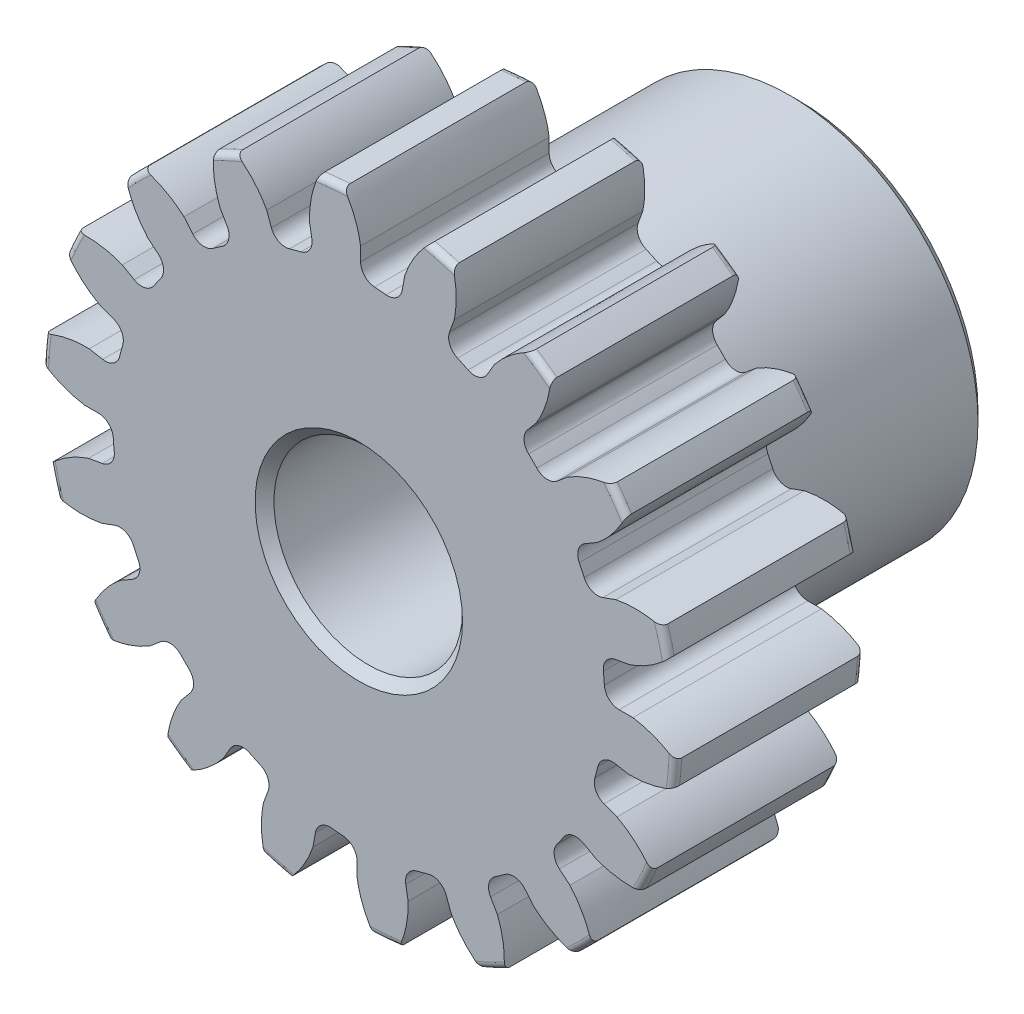
SolidWorks part; units mm, degrees
ref_plane "Front" through (0, 0, 0) normal (0, 0, 1) x (1, 0, 0)
ref_plane "Top" through (0, 0, 0) normal (0, 1, 0) x (1, 0, 0)
ref_plane "Right" through (0, 0, 0) normal (1, 0, 0) x (0, 0, -1)
sketch "Sketch1" plane through (0, 0, 0) normal (0, 0, 1) x (1, 0, 0)
  line L0 (-228.6, 0) -> (228.6, 0) construction
  circle A0 centre (0, 0) radius 8.001
  circle A1 centre (0, 0) radius 7.1501 construction
  circle A3 centre (0, 0) radius 6.2135 construction
  dimension "D1" = 1.7875
  dimension "OD" = 16.002
  dimension "Ptich Dia" = 14.3002
  dimension "Root Dia" = 12.4269
  dimension "D3" = 0.8509
  dimension "Number of Teeth" = 457.2
extrude "Boss-Extrude1" add sketch "Sketch1" against normal blind 4.7625
sketch "Sketch2" plane through (0, 0, 0) normal (1, 0, 0) x (0, 0, -1)
  line L0 (4.7625, 0) -> (11.1125, 0)
  line L1 (4.7625, 0) -> (4.7625, 4.7625)
  line L2 (4.7625, 4.7625) -> (11.1125, 4.7625)
  line L3 (11.1125, 4.7625) -> (11.1125, 0)
  point P5 (11.1125, -4.7625)
  point P6 (0, -8.001)
  point P7 (4.7625, -8.001)
  point P9 (0, 8.001)
  dimension "Face Wd" = 4.7625
  dimension "B Hub Dia" = 9.525
  dimension "D O'all Lg." = 11.1125
revolve "Revolve1" add sketch "Sketch2" angle 360 about L0
fillet "Fillet2" radius 0.16 3 edges at (8.001, 0, -4.7625) (8.001, 0, 0) (4.7625, 0, -4.7625)
sketch "Sketch3" plane through (0, 0, 0) normal (0, 0, 1) x (1, 0, 0)
  line L0 (0, 0) -> (0, 8.001) construction
  line L1 (-1.7332, 6.7019) -> (0, 7.1501)
  line L2 (-9.5921, 7.1501) -> (9.5921, 7.1501) construction
  line L3 (-9.2865, 4.7484) -> (9.2865, 9.5518) construction
  line L4 (-1.7332, 6.7019) -> (0, 0) construction
  line L5 (-4.4209, 5.3268) -> (0, 0) construction
  line L6 (-4.4209, 5.3268) -> (-0.7209, 8.3975) construction
  line L7 (-1.2086, 6.816) -> (0, 0) construction
  line L8 (-1.2086, 6.816) -> (0.0254, 7.0348) construction
  arc A0 (-1.7332, 6.7019) -> (-4.4209, 5.3268) centre (0, 0) ccw
  circle A1 centre (0, 0) radius 7.1501 construction
  circle A2 centre (0, 0) radius 6.9224 construction
  arc A3 (-1.7332, 6.7019) -> (-1.2086, 6.816) centre (0, 0) cw
  circle A4 centre (0, 0) radius 8.001 construction
  point P6 (0, 7.1501)
  dimension "D1" = 1.7902
  dimension "Pressure Angle" = 14.5
  dimension "D2" = 3.0434
  dimension "D3" = 4.8083
  dimension "D4" = 0.5371
  dimension "D5" = 1.2532
sketch "Sketch4" plane through (0, 0, 0) normal (0, 0, 1) x (1, 0, 0)
  line L0 (0, 0) -> (0.6208, 7.0958) construction
  line L1 (0.0448, 6.9222) -> (0.0448, 6.2133)
  line L2 (0, 7.1501) -> (1.2416, 7.0415) construction
  line L3 (1.1579, 6.8248) -> (1.0348, 6.1267)
  line L4 (0.0448, 6.2133) -> (0, 0) construction
  line L5 (0, 0) -> (0, 8.001) construction
  line L6 (-4.4209, 5.3268) -> (-0.7209, 8.3975) construction
  line L7 (-4.4209, 5.3268) -> (-0.7209, 8.3975) construction
  arc A0 (1.0348, 6.1267) -> (0.0448, 6.2133) centre (0, 0) ccw
  arc A1 (0, 7.1501) -> (1.2416, 7.0415) centre (0, 0) cw construction
  circle A2 centre (0, 0) radius 7.1501 construction
  circle A3 centre (0, 0) radius 6.9224 construction
  circle A4 centre (0, 0) radius 6.2135 construction
  arc A5 (2.1681, 8.1448) -> (-0.7209, 8.3975) centre (0, 0) ccw
  spline S0 degree 2 poles (-0.7209, 8.3975) (-0.0794, 7.7502) (0.0448, 6.9222) knots 0 0 0 1 1 1
  spline S1 degree 2 poles (2.1681, 8.1448) (1.424, 7.6187) (1.1579, 6.8248) knots 0 0 0 1 1 1
  dimension "D1" = 1.2479
extrude "Cut-Extrude1" cut sketch "Sketch4" against normal through all
fillet "Fillet1" radius 0.3744 2 edges at (1.0348, 6.1267, -2.3813) (0.0448, 6.2133, -2.3813)
pattern_circular "CirPattern1" count 18 over 360 about axis through (0, 0, -4.7625) along (0, 0, 1) of "Cut-Extrude1", "Fillet1"
sketch "Sketch5" plane through (0, 0, 0) normal (0, 0, 1) x (1, 0, 0)
  circle A0 centre (0, 0) radius 2.3813
  circle A1 centre (0, 0) radius 1.5875 construction
  dimension "Bore Min" = 4.7625
  dimension "Bore Max" = 3.175
extrude "Cut-Extrude2" cut sketch "Sketch5" against normal through all
chamfer "Chamfer1" distance 0.2381 angle 45 3 edges at (4.7625, 0, -11.1125) (2.3813, 0, 0) (2.3813, 0, -11.1125)
sketch "Pitch Dia" plane through (0, 0, 0) normal (0, 0, 1) x (1, 0, 0)
  circle A0 centre (0, 0) radius 7.1501 construction
  circle A1 centre (0, 0) radius 7.1501 construction
equation "\"D1@Boss-Extrude1\" = \"Face Wd@Sketch2\""
equation "\"D2@Sketch3\" = \"D1@Sketch3\"*1.7"
equation "\"D3@Sketch3\" = \"D1@Sketch3\"+\"D2@Sketch3\"-.001"
equation "\"D4@Sketch3\" = \"D1@Sketch3\"*.3"
equation "\"D5@Sketch3\" = \"D1@Sketch3\"-\"D4@Sketch3\""
equation "\"D1@Sketch4\" = 1.5708/(\"Number of Teeth@Sketch1\"/\"Ptich Dia@Sketch1\")"
equation "\"D1@Chamfer1\" = \"B Hub Dia@Sketch2\"*.025"
equation "\"D1@CirPattern1\" = \"Number of Teeth@Sketch1\""
equation "\"D1@Fillet1\" = \"D1@Sketch4\"*.3"
equation "\"D1@Fillet2\" = \"OD@Sketch1\"*.01"
equation "\"D1@Sketch1\" = 2.250/(\"Number of Teeth@Sketch1\"/\"Ptich Dia@Sketch1\")"
